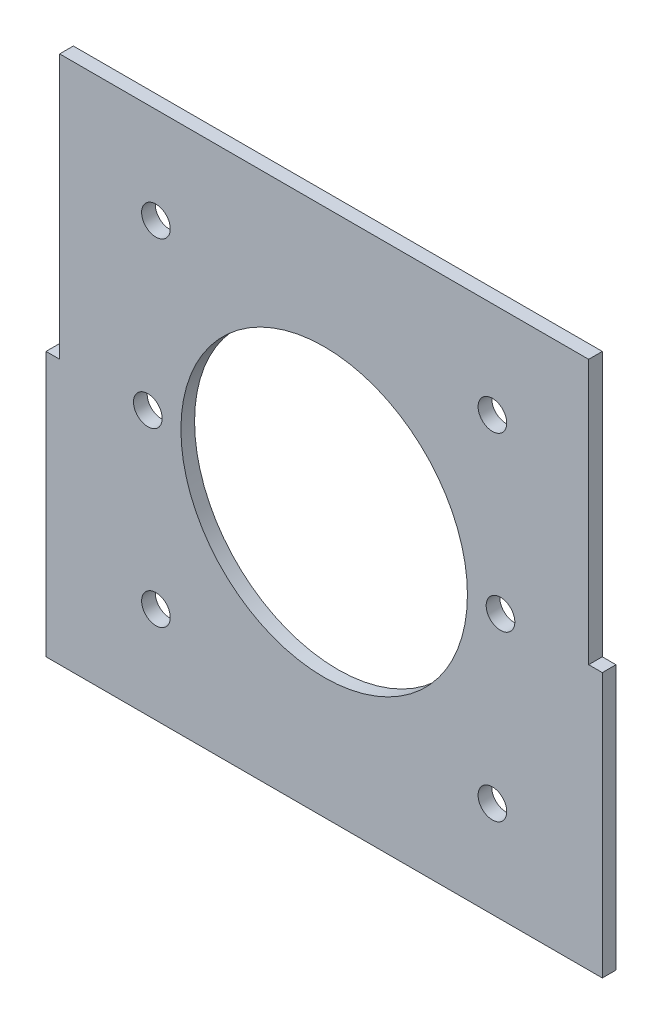
SolidWorks part; units mm, degrees
material "Teak"
ref_plane "Front Plane" through (0, 0, 0) normal (0, 0, 1) x (1, 0, 0)
ref_plane "Top Plane" through (0, 0, 0) normal (0, 1, 0) x (1, 0, 0)
ref_plane "Right Plane" through (0, 0, 0) normal (1, 0, 0) x (0, 0, -1)
sketch "Sketch1" plane through (0, 0, 0) normal (0, 0, 1) x (1, 0, 0)
  line L1 (-60, -60) -> (60, -60)
  line L2 (-60, -60) -> (-60, 60)
  line L3 (-60, 60) -> (60, 60)
  line L4 (60, -60) -> (60, 60)
  circle A0 centre (-38.1661, 38.1661) radius 3.25
  circle A1 centre (38.1661, 38.1661) radius 3.25
  circle A2 centre (38.1661, -38.1661) radius 3.25
  circle A3 centre (-38.1661, -38.1661) radius 3.25
  circle A9 centre (-40, 0) radius 3.25
  circle A10 centre (40, 0) radius 3.25
  dimension "D1" = 6.5
  dimension "D13" = 6.5
  dimension "D3" = 107.95
  dimension "D5" = 120
  dimension "D6" = 120
  dimension "D14" = 20
  dimension "D2" = 4
extrude "Boss-Extrude1" add sketch "Sketch1" along normal blind 3.1
sketch "Sketch2" plane through (0, 0, 3.1) normal (0, 0, 1) x (1, 0, 0)
  line L0 (60, 0) -> (60, -60)
  line L1 (60, 0) -> (63.1, 0)
  line L2 (60, -60) -> (63.1, -60)
  line L3 (63.1, 0) -> (63.1, -60)
  line L4 (60, -60) -> (60, 60) construction
  line L5 (0, 0) -> (0, -60) construction
  line L6 (-60, -60) -> (60, -60) construction
  line L7 (-63.1, 0) -> (-63.1, -60)
  line L8 (-60, -60) -> (-63.1, -60)
  line L9 (-60, 0) -> (-63.1, 0)
  line L10 (-60, 0) -> (-60, -60)
  dimension "D1" = 3.1
extrude "Boss-Extrude3" add sketch "Sketch2" against normal through all
sketch "Sketch4" plane through (0, 0, 3.1) normal (0, 0, 1) x (1, 0, 0)
  line L0 (0, 60) -> (0, -60) construction
  line L1 (60, 60) -> (-60, 60) construction
  line L2 (-63.1, -60) -> (63.1, -60) construction
  line L3 (0, -10.35) -> (47.052, -10.35) construction
  line L5 (-10.25, -30.7) -> (10.25, -30.7)
  line L6 (-10.25, -30.7) -> (-10.25, 10)
  line L7 (-10.25, 10) -> (10.25, 10)
  line L8 (10.25, -30.7) -> (10.25, 10)
  line L9 (-10.25, -30.7) -> (10.25, 10) construction
  line L12 (-10.25, 10) -> (10.25, -30.7) construction
  circle A0 centre (0, 0) radius 2.6097 construction
  circle A1 centre (5, 14.15) radius 2.5
  circle A2 centre (-5, 14.15) radius 2.5
  circle A3 centre (-5, -34.85) radius 2.5
  circle A4 centre (5, -34.85) radius 2.5
  point P9 (0, -10.35)
  dimension "D5" = 10
  dimension "D4" = 5
  dimension "D1" = 20.5
  dimension "D2" = 40.7
  dimension "D3" = 10
  dimension "D6" = 49
extrude "Cut-Extrude1" [suppressed] cut sketch "Sketch4" against normal through all
sketch "Sketch5" plane through (0, 0, 3.1) normal (0, 0, 1) x (1, 0, 0)
  circle A0 centre (0, 0) radius 32.5
  dimension "D1" = 65
extrude "Cut-Extrude2" cut sketch "Sketch5" against normal through all
sketch "Sketch6" [suppressed] plane through (0, 0, 0) normal (0, 0, 1) x (1, 0, 0)
  line L0 (-40, 40) -> (40, -40) construction
  line L1 (40, 40) -> (-40, -40) construction
  line L2 (-13.4704, 13.4704) -> (-13.4704, -13.4704) construction
  line L3 (-13.4704, 13.4704) -> (-11.4704, 13.4704) construction
  line L4 (0, 0) -> (57.4877, 0) construction
  line L5 (-11.4704, -13.4704) -> (-13.4704, -13.4704) construction
  line L6 (-15.4704, 13.4704) -> (-15.4704, -13.4704)
  line L7 (0, -40) -> (0, 40) construction
  line L8 (-15.4704, 13.4704) -> (-15.4704, 18.4704)
  line L9 (-15.4704, -13.4704) -> (-15.4704, -18.4704)
  line L10 (-11.4704, -13.4704) -> (-11.4704, -18.4704)
  line L11 (-11.4704, 13.4704) -> (-11.4704, -13.4704)
  line L12 (-11.4704, 13.4704) -> (-11.4704, 18.4704)
  line L13 (11.4704, -13.4704) -> (13.4704, -13.4704) construction
  line L14 (13.4704, 13.4704) -> (11.4704, 13.4704) construction
  line L19 (13.4704, 13.4704) -> (13.4704, -13.4704) construction
  line L20 (11.4704, 13.4704) -> (11.4704, 18.4704)
  line L21 (11.4704, 13.4704) -> (11.4704, -13.4704)
  line L22 (11.4704, -13.4704) -> (11.4704, -18.4704)
  line L23 (15.4704, -13.4704) -> (15.4704, -18.4704)
  line L24 (15.4704, 13.4704) -> (15.4704, 18.4704)
  line L25 (15.4704, 13.4704) -> (15.4704, -13.4704)
  arc A0 (-11.4704, 18.4704) -> (-15.4704, 18.4704) centre (-13.4704, 18.4704) ccw
  arc A1 (-15.4704, -18.4704) -> (-11.4704, -18.4704) centre (-13.4704, -18.4704) ccw
  arc A2 (15.4704, -18.4704) -> (11.4704, -18.4704) centre (13.4704, -18.4704) cw
  arc A3 (11.4704, 18.4704) -> (15.4704, 18.4704) centre (13.4704, 18.4704) cw
  circle A4 centre (0, 0) radius 9.525
  point P11 (0, 0)
  dimension "D1" = 26.9408
  dimension "D5" = 19.05
  dimension "D2" = 5
  dimension "D6" = 2
  dimension "D3" = 0
  dimension "D7" = 80
  dimension "D8" = 80
extrude "Cut-Extrude4" [suppressed] cut sketch "Sketch6" along normal through all
sketch "Sketch7" [suppressed] plane through (0, 0, 3.1) normal (0, 0, 1) x (1, 0, 0)
  line L0 (0, -15) -> (0, 0) construction
  line L1 (-14.75, -44.75) -> (-14.7459, 14.7418)
  line L2 (-14.75, -44.75) -> (14.7459, -44.7418)
  line L3 (14.7459, -44.7418) -> (14.7541, 14.7582)
  line L4 (-14.7459, 14.7418) -> (-5.0154, 14.7418)
  line L5 (-14.75, -44.75) -> (14.7541, 14.7582) construction
  line L6 (14.7459, -44.7418) -> (-14.7459, 14.7418) construction
  line L7 (0, -15) -> (26.3784, -15) construction
  line L8 (-5.0154, 14.7418) -> (-5, 16.65)
  line L9 (-5, 16.65) -> (5, 16.65)
  line L10 (5, 16.65) -> (5, 14.7582)
  line L11 (5, 14.7582) -> (14.7541, 14.7582)
  circle A0 centre (-8.75, 18.75) radius 2.5
  circle A1 centre (8.75, 18.75) radius 2.5
  circle A2 centre (8.75, -48.75) radius 2.5
  circle A3 centre (-8.75, -48.75) radius 2.5
  circle A5 centre (-5, 14.15) radius 2.5 construction
  circle A6 centre (5, 14.15) radius 2.5 construction
  point P0 (0, -15)
  dimension "D4" = 5
  dimension "D1" = 59.5
  dimension "D2" = 29.5
  dimension "D5" = 17.5
  dimension "D6" = 67.5
extrude "Cut-Extrude6" [suppressed] cut sketch "Sketch7" against normal through all
equation "\"thick\"= 3.1mm"
equation "\"small_bearing_outer\"=12.9mm"
equation "\"servo1_L\"=40.7mm"
equation "\"servo1_W\"=20.5mm"
equation "\"servo1_H\"=43.5mm"
equation "\"servo1_hL\"=49mm"
equation "\"servo1_hW\"=10mm"
equation "\"servo1_H2\"=27mm"
equation "\"large_bearing_inner\"=2.75in"
equation "\"large_bearing_outer\"=4.75in"
equation "\"large_bearing_thick\"=3/8in"
equation "\"large_bearing_h1\"=3.25in"
equation "\"large_bearing_h2\"=4.25in"
equation "\"D3@Sketch1\"=\"large_bearing_h2\""
equation "\"D6@Sketch1\"=\"D5@Sketch1\""
equation "\"D1@Sketch2\"=\"thick\""
equation "\"D1@Sketch4\"=\"servo1_W\""
equation "\"D2@Sketch4\"=\"servo1_L\""
equation "\"D5@Sketch4\"=\"servo1_hW\""
equation "\"D6@Sketch4\"=\"servo1_hL\""
equation "\"servo2_L\"=59.5mm"
equation "\"servo2_W\"=29.5mm"
equation "\"servo2_hL\"=67.5mm"
equation "\"D1@Sketch7\"=\"servo2_L\""
equation "\"D2@Sketch7\"=\"servo2_W\""
equation "\"servo2_hW\"=17.5mm"
equation "\"D5@Sketch7\"=\"servo2_hW\""
equation "\"D6@Sketch7\"=\"servo2_hL\""
